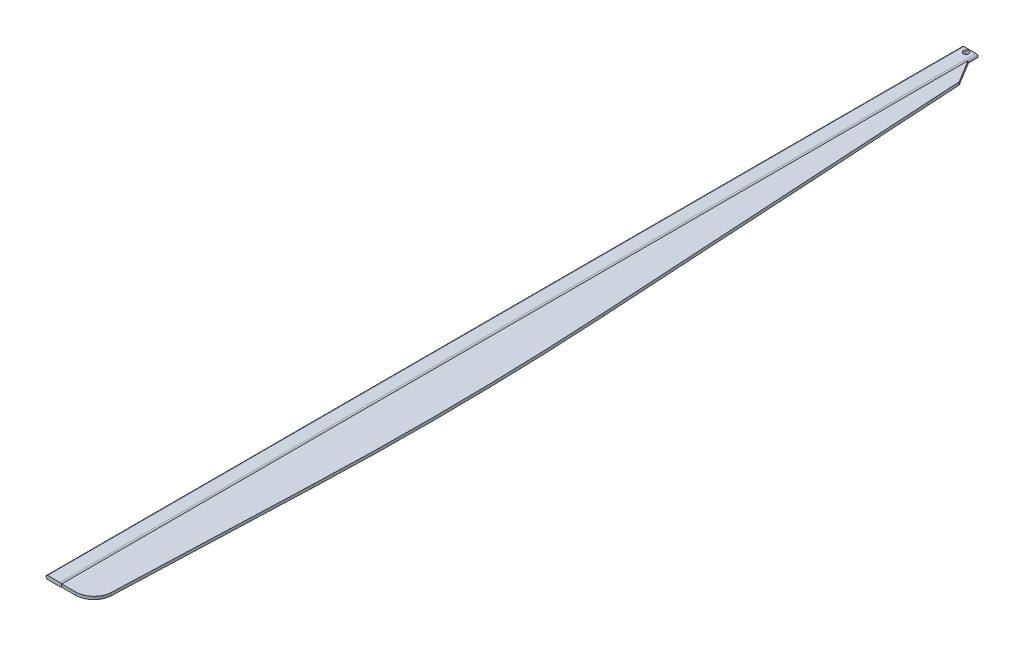
SolidWorks part; units mm, degrees
material "Wrought Stainless Steel"
ref_plane "Front Plane" through (0, 0, 0) normal (0, 0, 1) x (1, 0, 0)
ref_plane "Top Plane" through (0, 0, 0) normal (0, 1, 0) x (1, 0, 0)
ref_plane "Right Plane" through (0, 0, 0) normal (1, 0, 0) x (0, 0, -1)
sketch "Sketch1" plane through (0, 0, 0) normal (0, 0, 1) x (1, 0, 0)
  line L0 (-165, 0) -> (165, 0) construction
  line L1 (-165, 50) -> (165, 50)
  line L2 (-165, -50) -> (165, -50)
  arc A0 (-165, 50) -> (-165, -50) centre (-165, 0) ccw
  arc A1 (165, -50) -> (165, 50) centre (165, 0) ccw
  point P3 (0, 0)
  point P8 (-215, 0)
  point P9 (215, 0)
  dimension "D2" = 100
  dimension "D1" = 430
sketch "Sketch2" plane through (0, 0, 0) normal (0, 1, 0) x (1, 0, 0)
  line L0 (0, 0) -> (0, -25000)
  dimension "D1" = 25000
sweep "Sweep1" add profiles "Sketch1" path "Sketch2"
sketch "Sketch3" plane through (0, 0, 0) normal (0, 1, 0) x (1, 0, 0)
  line L0 (215, -281.2091) -> (591.0525, -901.5244)
  line L1 (591.0525, -901.5244) -> (1200.8515, -11226.0791)
  line L2 (1288.0886, -19204.7473) -> (1090.7079, -24518.5596)
  line L3 (591.0525, -25000) -> (215, -25000)
  line L5 (215, -281.2091) -> (215, -25000)
  line L9 (215, -25000) -> (215, 0) construction
  arc A0 (1200.8515, -11226.0791) -> (1288.0886, -19204.7473) centre (-81697.0591, -16122.2777) cw
  arc A1 (1090.7079, -24518.5596) -> (591.0525, -25000) centre (591.0525, -24500) cw
  dimension "D2" = 500
sketch "Sketch4" plane through (0, 50, 0) normal (0, 1, 0) x (1, 0, 0)
  line L0 (0, 0) -> (0, -120) construction
  line L1 (165, 0) -> (-165, 0) construction
  circle A0 centre (0, -120) radius 75
  dimension "D1" = 150
  dimension "D2" = 120
extrude "Cut-Extrude1" cut sketch "Sketch4" against normal through all
fillet "Fillet1" radius 20 4 edges at (0, 50, 0) (215, 0, 0) (0, -50, 0) (-215, 0, 0)
extrude "Boss-Extrude1" add sketch "Sketch3" along normal blind 40 and the other way blind 40 separate body
